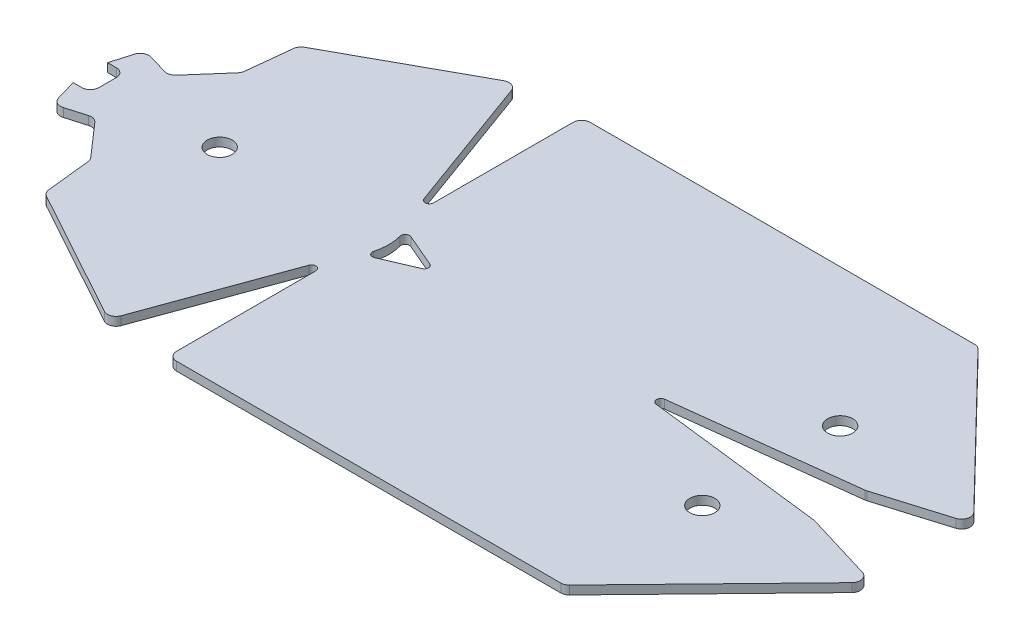
SolidWorks part; units mm, degrees
material "ABS"
ref_plane "Front" through (0, 0, 0) normal (0, 0, 1) x (1, 0, 0)
ref_plane "Top" through (0, 0, 0) normal (0, 1, 0) x (1, 0, 0)
ref_plane "Right" through (0, 0, 0) normal (1, 0, 0) x (0, 0, -1)
sketch "Sketch1" plane through (0, 0, 0) normal (0, 1, 0) x (1, 0, 0)
  line L1 (-40, -19) -> (40, -19)
  line L2 (-40, -19) -> (-40, 19)
  line L3 (-40, 19) -> (40, 19)
  line L4 (40, -19) -> (40, 19)
  line L5 (-40, -19) -> (40, 19) construction
  line L6 (-40, 19) -> (40, -19) construction
  point P0 (0, 0)
  dimension "D1" = 38
  dimension "D2" = 80
sketch "Sketch5" plane through (0, 0, 0) normal (0, 1, 0) x (1, 0, 0)
  line L0 (0, 0) -> (0, 506.6667) construction
sketch "Sketch6" plane through (0, 0, 0) normal (0, 1, 0) x (1, 0, 0)
  line L0 (32, 24) -> (49.571, 5.8975)
  line L1 (-14, 24) -> (40, 24)
  line L2 (-14, 24) -> (-14, 3)
  line L3 (-14, 3) -> (40, 3) construction
  line L4 (40, 24) -> (40, 3)
  line L5 (-14, 24) -> (40, 3) construction
  line L6 (-14, 3) -> (40, 24) construction
  line L11 (-45, 0) -> (-7, 0)
  line L12 (40, -3) -> (15, 0)
  line L13 (40, 3) -> (15, 0)
  line L15 (15, 0) -> (-7, 0)
  line L16 (15, 0) -> (40, 0)
  line L17 (-7, 0) -> (-14, 3)
  line L18 (-7, 0) -> (-14, -3)
  line L19 (40, -19) -> (40, 19) construction
  line L21 (-45, -2) -> (-45, 2)
  line L22 (-21.1824, 23.7335) -> (-37.5799, 14.7228)
  line L23 (-37.5799, 14.7228) -> (-38.229, 8.758)
  line L24 (-38.229, 8.758) -> (-42.182, 4.2442)
  line L25 (-42.182, 4.2442) -> (-46.0229, 5.3609)
  line L26 (-46.0229, 5.3609) -> (-47, 2)
  line L27 (-47, 2) -> (-45, 2)
  line L28 (-21.1824, 23.7335) -> (-14, 4)
  line L29 (-14, -3) -> (40, -24) construction
  line L30 (-14, -24) -> (40, -3) construction
  line L31 (-14, -3) -> (40, -3) construction
  line L32 (-21.1824, -23.7335) -> (-14, -4)
  line L33 (-47, -2) -> (-45, -2)
  line L34 (-46.0229, -5.3609) -> (-47, -2)
  line L35 (-42.182, -4.2442) -> (-46.0229, -5.3609)
  line L36 (-38.229, -8.758) -> (-42.182, -4.2442)
  line L37 (-37.5799, -14.7228) -> (-38.229, -8.758)
  line L38 (-21.1824, -23.7335) -> (-37.5799, -14.7228)
  line L39 (40, -24) -> (40, -3)
  line L40 (-14, -24) -> (-14, -3)
  line L41 (-14, -24) -> (40, -24)
  line L42 (32, -24) -> (49.571, -5.8975)
  line L43 (49.571, 5.8975) -> (40, 3)
  line L44 (49.571, -5.8975) -> (40, -3)
  line L46 (-40, 19) -> (40, 19) construction
  arc A0 (-14, 4) -> (-14, -4) centre (-18.2021, 0) cw
  point P0 (13, 13.5)
  point P5 (13, -13.5)
  point P18 (40, 0)
  dimension "D6" = 5.8015
  dimension "D8" = 4
  dimension "D1" = 54
  dimension "D2" = 3
  dimension "D3" = 25
  dimension "D4" = 38
  dimension "D5" = 7
  dimension "D7" = 5
  dimension "D9" = 21
  dimension "D10" = 125
  dimension "D11" = 145
  dimension "D12" = 115
  dimension "D13" = 2
  dimension "D14" = 3.5
  dimension "D15" = 4
  dimension "D16" = 6
  dimension "D17" = 6
  dimension "D18" = 170
  dimension "D19" = 10
  dimension "D20" = 2
  dimension "D21" = 20
  dimension "D22" = 8
extrude "Boss-Extrude2" add sketch "Sketch6" along normal blind 1 contours L18 A0 L40 L41 L42 L39 L12 L15 | L42 L44 L39 | A0 L18 L40 | A0 L11 L21 L33 L34 L35 L36 L37 L38 L32 L40 L18 | L2 A0 L17 L15 L13 L4 L0 L1 | L43 L0 L4
fillet "Fillet1" radius 1 20 edges at (-46.0229, 0.5, -5.3609) (-46.0229, 0.5, 5.3609) (-45, 0.5, 2) (-45, 0.5, -2) (-42.182, 0.5, -4.2442) (-38.229, 0.5, 8.758) (-42.182, 0.5, 4.2442) (-38.229, 0.5, -8.758) (-37.5799, 0.5, -14.7228) (-37.5799, 0.5, 14.7228) (-21.1824, 0.5, 23.7335) (-14, 0.5, 24) (40, 0.5, -3) (40, 0.5, 3) (-14, 0.5, -24) (-21.1824, 0.5, -23.7335) (32, 0.5, 24) (32, 0.5, -24) (49.571, 0.5, 5.8975) (49.571, 0.5, -5.8975)
fillet "Fillet2" radius 0.5 6 edges at (15, 0.5, 0) (-14, 0.5, 4) (-14, 0.5, -4) (-13.002, 0.5, 2.5723) (-7, 0.5, 0) (-13.002, 0.5, -2.5723)
sketch "Sketch7" plane through (0, 1, 0) normal (0, 1, 0) x (1, 0, 0)
  line L0 (-14, -8) -> (32, -8)
  line L1 (-14, -23) -> (-14, -6.8356) construction
  line L2 (32, -8) -> (32, -24)
  line L3 (-13, -24) -> (31.577, -24) construction
  line L4 (-45, 0) -> (-32, 0)
  line L5 (-45, -1) -> (-45, 1) construction
  line L6 (-32, 0) -> (-32, -24)
  line L7 (-50, 0) -> (50, 0) construction
  line L8 (32, 8) -> (32, 24)
  line L9 (-14, 8) -> (32, 8)
  dimension "D1" = 13
  dimension "D2" = 46
  dimension "D3" = 16
hole_wizard "M2.5 Clearance Hole1" positions "Sketch8" profile "Sketch9" hole size "M2.5" standard "ANSI Metric"
sketch "Sketch8" plane through (0, 1, 0) normal (0, 1, 0) x (1, 0, 0)
  point P0 (-32, 0)
  point P3 (32, 8)
  point P6 (32, -8)
sketch "Sketch9" plane through (-32, 1, 0) normal (1, 0, 0) x (0, 0, 1)
  line L0 (0, 0) -> (0, 8.1212)
  line L1 (0, 8.1212) -> (1.45, 7.25)
  line L2 (1.45, 7.25) -> (1.45, 0)
  line L5 (1.45, 0) -> (0, 0)
  line L10 (0, 8.1212) -> (-1.45, 7.25) construction
  line L11 (0, -6.35) -> (0, 107.95) construction
  dimension "Hole Dia." = 2.9
  dimension "Hole Depth" = 7.25
  dimension "Drill Angle" = 118
